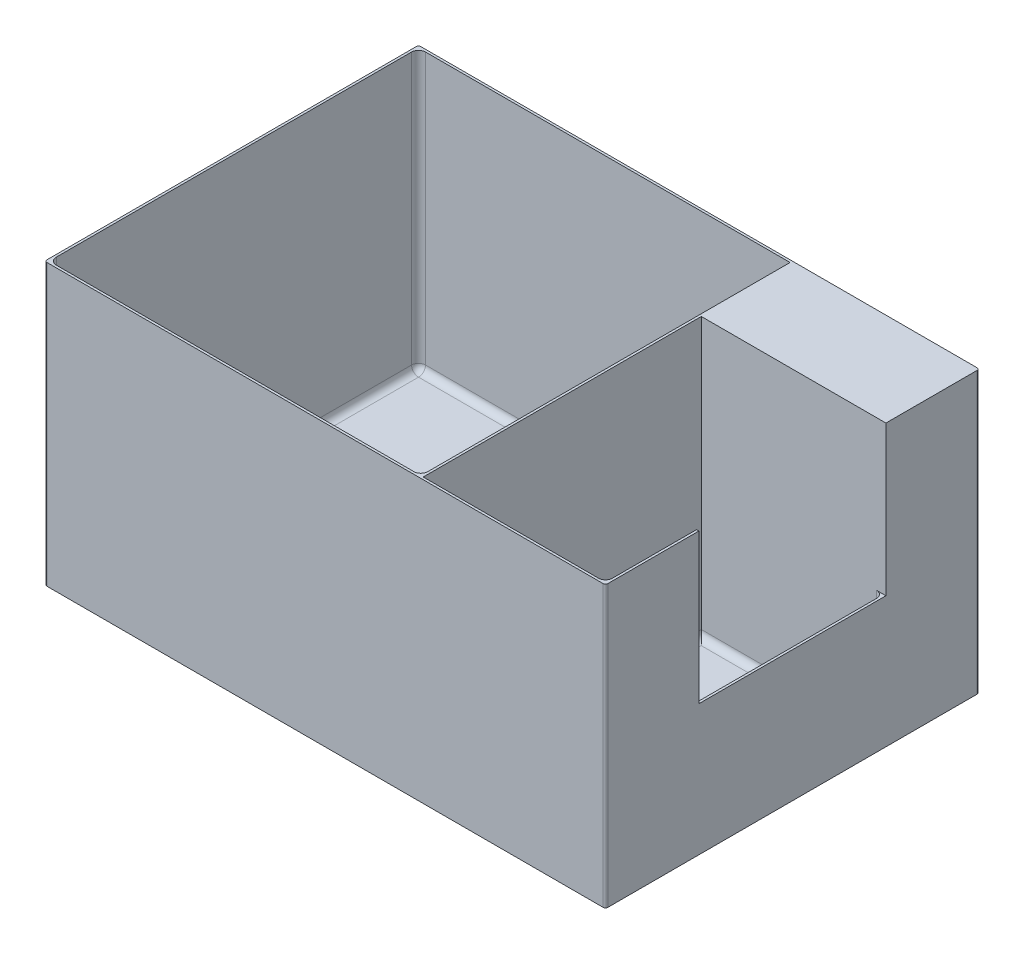
SolidWorks part; units mm, degrees
ref_plane "前基準面" through (0, 0, 0) normal (0, 0, 1) x (1, 0, 0)
ref_plane "上基準面" through (0, 0, 0) normal (0, 1, 0) x (1, 0, 0)
ref_plane "右基準面" through (0, 0, 0) normal (1, 0, 0) x (0, 0, -1)
sketch "草圖1" plane through (0, 0, 0) normal (0, 1, 0) x (1, 0, 0)
  line L1 (-120, -80) -> (120, -80)
  line L2 (-120, -80) -> (-120, 80)
  line L3 (-120, 80) -> (120, 80)
  line L4 (120, -80) -> (120, 80)
  line L5 (-120, -80) -> (120, 80) construction
  line L6 (-120, 80) -> (120, -80) construction
  point P0 (0, 0)
  dimension "D1" = 240
  dimension "D2" = 160
extrude "填料-伸長1" add sketch "草圖1" along normal blind 120
sketch "草圖2" plane through (0, 120, 0) normal (0, 1, 0) x (1, 0, 0)
  line L0 (-66, 0) -> (66, 0) construction
  line L1 (-119, -79) -> (40, -79)
  line L2 (-119, -79) -> (-119, 79)
  line L3 (-119, 79) -> (40, 79)
  line L4 (40, -79) -> (40, 79)
  line L5 (-119, -79) -> (40, 79) construction
  line L6 (-119, 79) -> (40, -79) construction
  line L7 (-120, 80) -> (-120, -80) construction
  line L8 (120, 80) -> (-120, 80) construction
  line L9 (120, -80) -> (120, 80) construction
  line L11 (41, -79) -> (119, -79)
  line L12 (41, -79) -> (41, 40)
  line L13 (41, 40) -> (119, 40)
  line L14 (119, -79) -> (119, 40)
  line L15 (41, -79) -> (119, 40) construction
  line L16 (41, 40) -> (119, -79) construction
  line L17 (-120, -80) -> (120, -80) construction
  point P0 (-39.5, 0)
  point P13 (88, 0)
  point P18 (0, 0)
  point P23 (56.7224, -78)
  dimension "D1" = 1
  dimension "D2" = 1
  dimension "D3" = 80
  dimension "D4" = 40
  dimension "D5" = 1
  dimension "D6" = 1
  dimension "D7" = 1
extrude "除料-伸長1" cut sketch "草圖2" against normal blind 119
sketch "草圖3" plane through (120, 0, 0) normal (1, 0, 0) x (0, 0, -1)
  line L0 (0, 66) -> (0, -66) construction
  line L1 (-40, 56) -> (40, 56)
  line L2 (-40, 56) -> (-40, 120)
  line L3 (-40, 120) -> (40, 120)
  line L4 (40, 56) -> (40, 120)
  line L5 (-40, 56) -> (40, 120) construction
  line L6 (-40, 120) -> (40, 56) construction
  line L7 (-80, 120) -> (80, 120) construction
  point P0 (0, 88)
  dimension "D1" = 64
  dimension "D2" = 80
extrude "除料-伸長2" cut sketch "草圖3" against normal up to next
fillet "圓角1" radius 1 4 edges at (-120, 60, -80) (120, 60, -80) (-120, 60, 80) (120, 60, 80)
fillet "圓角2" radius 3 13 edges at (-119, 60.5, 79) (-119, 60.5, -79) (119, 28.5, -40) (119, 60.5, 79) (-39.5, 1, 79) (80, 1, 79) (119, 1, 19.5) (40, 1, 0) (80, 1, -40) (41, 1, 19.5) (-119, 1, 0) (-39.5, 1, -79) (40, 60.5, 79)
